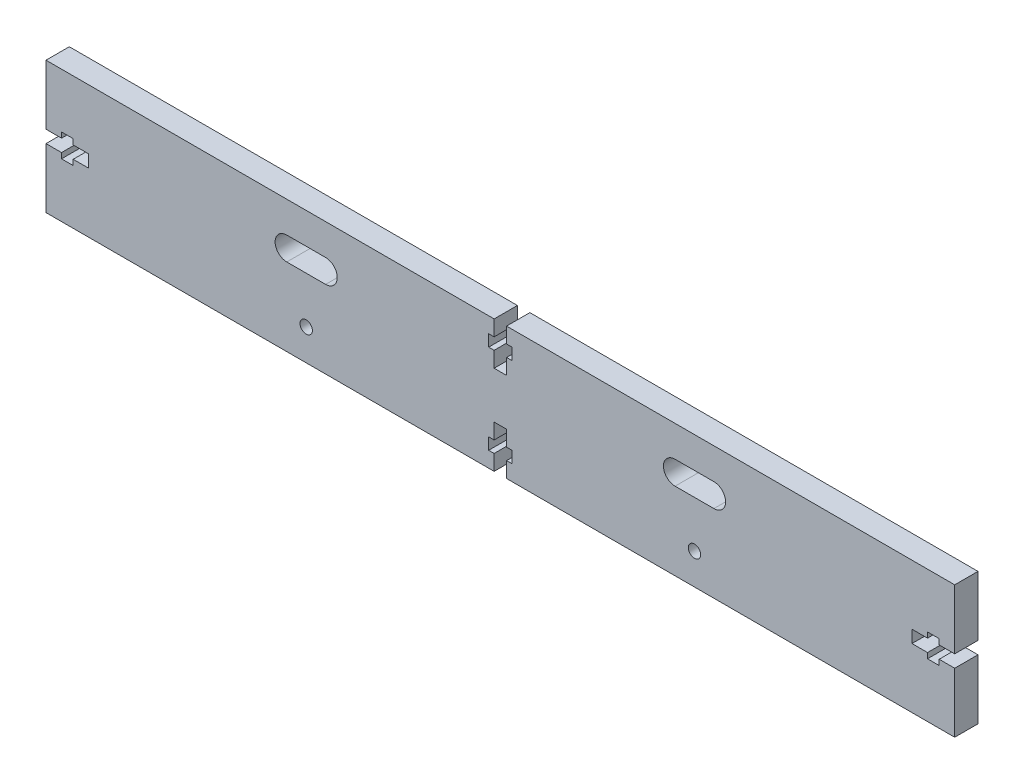
SolidWorks part; units mm, degrees
material "Balsa"
ref_plane "Plano frontal" through (0, 0, 0) normal (0, 0, 1) x (1, 0, 0)
ref_plane "Plano superior" through (0, 0, 0) normal (0, 1, 0) x (1, 0, 0)
ref_plane "Plano direito" through (0, 0, 0) normal (1, 0, 0) x (0, 0, -1)
sketch "Esboço1" plane through (0, 0, 0) normal (0, 0, 1) x (1, 0, 0)
  line L0 (-117, 0) -> (117, 0) construction
  line L1 (117, 17) -> (117, 1.6)
  line L2 (-117, 17) -> (-1.6, 17)
  line L3 (-117, 1.6) -> (-113, 1.6)
  line L4 (-113, 1.6) -> (-113, 3)
  line L5 (-113, 3) -> (-110, 3)
  line L6 (-110, 3) -> (-110, 1.6)
  line L7 (-110, 1.6) -> (-106, 1.6)
  line L8 (-106, 1.6) -> (-106, -1.6)
  line L9 (-106, -1.6) -> (-110, -1.6)
  line L10 (-110, -1.6) -> (-110, -3)
  line L11 (-110, -3) -> (-113, -3)
  line L12 (-113, -3) -> (-113, -1.6)
  line L13 (-113, -1.6) -> (-117, -1.6)
  line L14 (117, -17) -> (1.6, -17)
  line L15 (0, 0) -> (0, -24.9119) construction
  line L16 (-106, 0) -> (-106.252, 0) construction
  line L17 (-117, 1.6) -> (-117, 17)
  line L18 (-117, -1.6) -> (-117, -17)
  line L19 (-55, 6) -> (-45, 6) construction
  line L20 (-55, 9) -> (-45, 9)
  line L21 (-55, 3) -> (-45, 3)
  line L22 (55, 6) -> (45, 6) construction
  line L23 (55, 9) -> (45, 9)
  line L24 (55, 3) -> (45, 3)
  line L32 (106, 0) -> (106.252, 0) construction
  line L45 (113, -1.6) -> (117, -1.6)
  line L46 (113, -3) -> (113, -1.6)
  line L47 (110, -3) -> (113, -3)
  line L48 (110, -1.6) -> (110, -3)
  line L49 (106, -1.6) -> (110, -1.6)
  line L50 (106, 1.6) -> (106, -1.6)
  line L51 (110, 1.6) -> (106, 1.6)
  line L52 (110, 3) -> (110, 1.6)
  line L53 (113, 3) -> (110, 3)
  line L54 (113, 1.6) -> (113, 3)
  line L55 (117, 1.6) -> (113, 1.6)
  line L56 (117, -17) -> (117, -1.6)
  line L60 (117, -1.6) -> (117, -17)
  line L61 (-1.6, -17) -> (-1.6, -13)
  line L62 (-1.6, -13) -> (-3, -13)
  line L63 (-3, -13) -> (-3, -10)
  line L64 (-3, -10) -> (-1.6, -10)
  line L65 (-1.6, -10) -> (-1.6, -6)
  line L66 (-1.6, -6) -> (1.6, -6)
  line L67 (1.6, -6) -> (1.6, -10)
  line L68 (1.6, -10) -> (3, -10)
  line L69 (3, -10) -> (3, -13)
  line L70 (3, -13) -> (1.6, -13)
  line L71 (1.6, -13) -> (1.6, -17)
  line L72 (0, -6) -> (0, -17.7088) construction
  line L73 (-1.6, -17) -> (-117, -17)
  line L74 (0, 6) -> (0, 17.7088) construction
  line L75 (1.6, 13) -> (1.6, 17)
  line L76 (3, 13) -> (1.6, 13)
  line L77 (3, 10) -> (3, 13)
  line L78 (1.6, 10) -> (3, 10)
  line L79 (1.6, 6) -> (1.6, 10)
  line L80 (-1.6, 6) -> (1.6, 6)
  line L81 (-1.6, 10) -> (-1.6, 6)
  line L82 (-3, 10) -> (-1.6, 10)
  line L83 (-3, 13) -> (-3, 10)
  line L84 (-1.6, 13) -> (-3, 13)
  line L85 (-1.6, 17) -> (-1.6, 13)
  line L86 (1.6, 17) -> (117, 17)
  circle A0 centre (-50, -9) radius 1.6
  circle A1 centre (50, -9) radius 1.6
  arc A2 (-55, 9) -> (-55, 3) centre (-55, 6) ccw
  arc A3 (-45, 3) -> (-45, 9) centre (-45, 6) ccw
  arc A4 (55, 9) -> (55, 3) centre (55, 6) cw
  arc A5 (45, 3) -> (45, 9) centre (45, 6) cw
  point P28 (-50, 6)
  point P33 (0, 0)
  point P36 (50, 6)
  dimension "D13" = 3.2
  dimension "D15" = 3
  dimension "D1" = 4
  dimension "D2" = 3.2
  dimension "D3" = 3
  dimension "D4" = 6
  dimension "D5" = 17
  dimension "D6" = 234
  dimension "D7" = 17
  dimension "D8" = 4
  dimension "D9" = 4
  dimension "D10" = 3
  dimension "D11" = 8
  dimension "D12" = 4
  dimension "D14" = 50
  dimension "D16" = 10
extrude "Ressalto-extrusão1" add sketch "Esboço1" along normal blind 6
